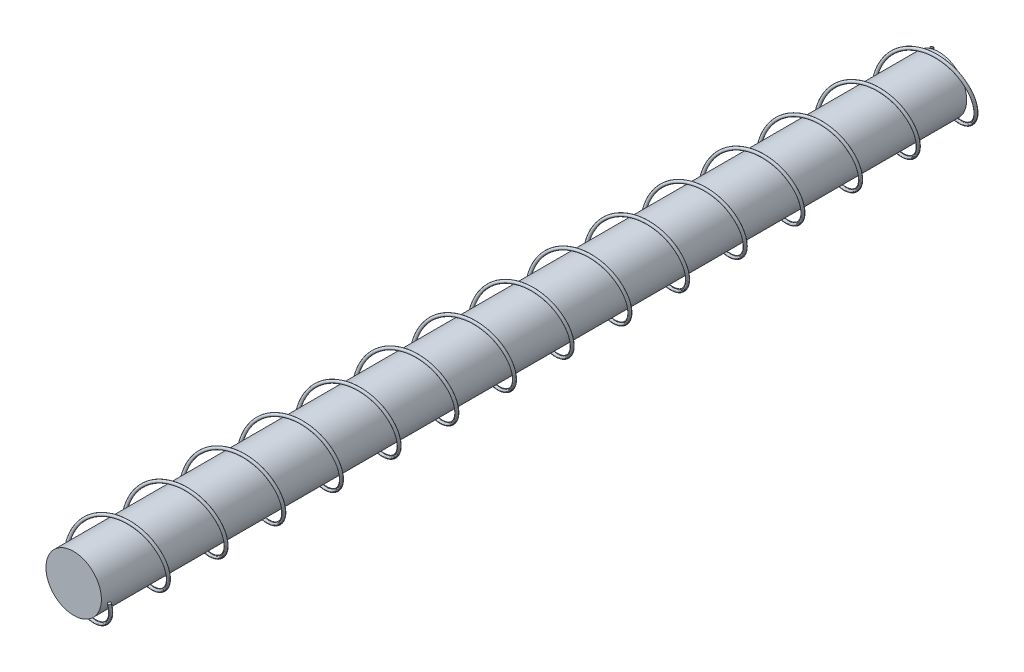
SolidWorks part; units mm, degrees
ref_plane "Ön Düzlem" through (0, 0, 0) normal (0, 0, 1) x (1, 0, 0)
ref_plane "Üst Düzlem" through (0, 0, 0) normal (0, 1, 0) x (1, 0, 0)
ref_plane "Sağ Düzlem" through (0, 0, 0) normal (1, 0, 0) x (0, 0, -1)
sketch "Çizim1" plane through (0, 0, 0) normal (0, 0, 1) x (1, 0, 0)
  circle A0 centre (0, 0) radius 0.9615
extrude "Yükseklik-Ekstrüzyon1" add sketch "Çizim1" along normal blind 30
sketch "Çizim3" plane through (0, 0, 30) normal (0, 0, 1) x (1, 0, 0)
  circle A0 centre (0, 0) radius 1.2377
curve "Helis/Spiral1" pitch 2 height 31 turns 15.5
ref_plane "Düzlem1" through (-1.2375, -0.0216, -1) normal (-0.0169, 0.9683, -0.2491) x (0.9999, 0.0164, -0.0042)
sketch "Çizim4" plane through (-1.2375, -0.0216, -1) normal (-0.0169, 0.9683, -0.2491) x (0.9999, 0.0164, -0.0042)
  circle A0 centre (0, 0) radius 0.0501
  spline S0 degree 3 poles (-1993.2342, 94.3185) (-8.8057, -58.5607) (4.8864, -32.4301) (2.1202, -29.6562) (2.0249, -29.5929) (1.7281, -29.4281) (1.5138, -29.3505) (1.0797, -29.2226) (0.8583, -29.1737) (0.4122, -29.0976) (0.1872, -29.0692) (-0.067, -29.056) (-0.0953, -29.0547) (-0.1254, -29.0543) (-0.1255, -29.0543) (-0.1184, -29.0543) (-0.106, -29.0541) (-0.0795, -29.0535) (-0.0583, -29.0528) (0.0123, -29.0498) (0.0688, -29.0461) (0.238, -29.0327) (0.3505, -29.0204) (0.6869, -28.9751) (0.9098, -28.934) (1.3491, -28.825) (1.5663, -28.758) (1.8763, -28.6197) (1.9772, -28.5672) (2.1634, -28.4387) (2.2518, -28.3624) (2.3343, -28.2141) (2.352, -28.1586) (2.3545, -28.0455) (2.3391, -27.9892) (2.2617, -27.8382) (2.1747, -27.7599) (1.9907, -27.6282) (1.8906, -27.5744) (1.6851, -27.4795) (1.5794, -27.4387) (1.2579, -27.3298) (1.0379, -27.2745) (0.594, -27.1864) (0.3697, -27.1535) (0.088, -27.1281) (0.0316, -27.1238) (-0.0532, -27.1193) (-0.0814, -27.118) (-0.1115, -27.1174) (-0.1132, -27.1174) (-0.1168, -27.1174) (-0.1172, -27.1174) (-0.1119, -27.1173) (-0.1013, -27.1172) (-0.0766, -27.1167) (-0.0554, -27.116) (0.0718, -27.1109) (0.1846, -27.1015) (0.5222, -27.0652) (0.746, -27.0296) (1.1884, -26.9344) (1.4075, -26.875) (1.7252, -26.7553) (1.8292, -26.7103) (2.0286, -26.6032) (2.1248, -26.5415) (2.2474, -26.424) (2.2844, -26.3805) (2.3406, -26.2822) (2.3592, -26.2271) (2.3638, -26.114) (2.3494, -26.0575) (2.2991, -25.9562) (2.264, -25.9109) (2.1459, -25.789) (2.051, -25.7249) (1.8538, -25.6139) (1.7504, -25.5671) (1.4347, -25.4426) (1.2163, -25.3804) (0.7751, -25.2797) (0.5517, -25.2415) (0.2147, -25.2011) (0.102, -25.1904) (-0.0393, -25.1826) (-0.0711, -25.1811) (-0.1029, -25.1805) (-0.1082, -25.1804) (-0.109, -25.1804) (-0.1055, -25.1804) (-0.0966, -25.1803) (-0.0736, -25.1799) (-0.0524, -25.1792) (0.0182, -25.1765) (0.0747, -25.173) (0.3567, -25.1512) (0.5813, -25.1208) (1.0263, -25.0381) (1.2469, -24.9856) (1.5699, -24.8812) (1.6763, -24.842) (1.8833, -24.7506) (1.9844, -24.6987) (2.1718, -24.5718) (2.2608, -24.4967) (2.3469, -24.3504) (2.3664, -24.2956) (2.373, -24.1826) (2.3595, -24.1258) (2.2861, -23.9728) (2.1999, -23.8932) (2.017, -23.7599) (1.9171, -23.7055) (1.6096, -23.5619) (1.3932, -23.492) (0.9554, -23.3774) (0.733, -23.3336) (0.3971, -23.2843) (0.2848, -23.2706) (0.1158, -23.2551) (0.0594, -23.2507) (-0.0254, -23.2459) (-0.0572, -23.2444) (-0.089, -23.2436) (-0.096, -23.2435) (-0.1025, -23.2435) (-0.0919, -23.2434) (-0.0848, -23.2433) (-0.0636, -23.2429) (-0.0495, -23.2425) (0.1908, -23.2336) (0.4161, -23.2076) (0.8631, -23.1368) (1.085, -23.0906) (1.5208, -22.9684) (1.7361, -22.8939) (2.0361, -22.7351) (2.1327, -22.674) (2.2568, -22.5582) (2.2946, -22.5153) (2.3531, -22.4185) (2.3734, -22.364) (2.382, -22.2512) (2.3696, -22.1941) (2.322, -22.0915) (2.2878, -22.0455) (2.1715, -21.9219) (2.077, -21.857) (1.7822, -21.6887) (1.5682, -21.61) (1.1347, -21.48) (0.9135, -21.4303) (0.4676, -21.3527) (0.2427, -21.324) (-0.0115, -21.3092) (-0.0397, -21.3078) (-0.0751, -21.3068) (-0.083, -21.3066) (-0.091, -21.3065) (-0.0928, -21.3065) (-0.0916, -21.3065) (-0.0854, -21.3065) (-0.066, -21.3062) (-0.0466, -21.3057) (0.0241, -21.3032) (0.0806, -21.2998) (0.2498, -21.2871) (0.3624, -21.2751) (0.699, -21.2309) (0.922, -21.1905) (1.3617, -21.0833) (1.5792, -21.0173) (1.8903, -20.8816) (1.9916, -20.8302) (2.18, -20.7048) (2.2697, -20.6308) (2.3592, -20.4866) (2.3804, -20.4324) (2.391, -20.3198) (2.3796, -20.2625) (2.3103, -20.1075) (2.225, -20.0266) (2.0433, -19.8917) (1.9437, -19.8367) (1.7391, -19.7401) (1.6336, -19.6986) (1.3127, -19.5879) (1.0929, -19.5318) (0.6493, -19.4421) (0.4252, -19.4085) (0.1436, -19.3821) (0.0871, -19.3776) (0.0024, -19.3725) (-0.0329, -19.3708) (-0.0682, -19.3698) (-0.0788, -19.3696) (-0.086, -19.3696) (-0.079, -19.3695) (-0.0613, -19.3694) (-0.0436, -19.3689) (0.0836, -19.3647) (0.1965, -19.3556) (0.5341, -19.3205) (0.758, -19.2856) (1.2008, -19.1919) (1.4201, -19.1335) (1.7386, -19.0159) (1.8429, -18.9716) (2.0435, -18.8668) (2.1405, -18.8064) (2.266, -18.6923) (2.3045, -18.65) (2.3652, -18.5546) (2.3872, -18.5008) (2.3998, -18.3884) (2.3895, -18.3309) (2.3448, -18.227) (2.3115, -18.1802) (2.1971, -18.0548) (2.103, -17.9892) (1.9072, -17.8757) (1.8042, -17.8281) (1.4893, -17.7014) (1.2712, -17.6383) (0.8303, -17.5359) (0.6071, -17.497) (0.2702, -17.4555) (0.1575, -17.4445) (0.0163, -17.4359) (-0.019, -17.4341) (-0.0579, -17.4329) (-0.0685, -17.4327) (-0.0738, -17.4326) (-0.076, -17.4326) (-0.0725, -17.4326) (-0.0565, -17.4325) (-0.0406, -17.4321) (0.0301, -17.4299) (0.0865, -17.4266) (0.3687, -17.4059) (0.5934, -17.3762) (1.0386, -17.295) (1.2594, -17.2433) (1.583, -17.1406) (1.6895, -17.1021) (1.8973, -17.0124) (1.9989, -16.9615) (2.1882, -16.8376) (2.2785, -16.7647) (2.3713, -16.6225) (2.394, -16.5692) (2.4086, -16.457) (2.3993, -16.3992) (2.3344, -16.2424) (2.2499, -16.1601) (2.0695, -16.0235) (1.9702, -15.968) (1.6639, -15.8216) (1.4479, -15.7507) (1.0105, -15.6343) (0.7882, -15.5898) (0.4525, -15.5393) (0.3402, -15.5253) (0.1713, -15.5091) (0.1149, -15.5045) (0.0302, -15.4992) (-0.0051, -15.4974) (-0.044, -15.4961) (-0.0564, -15.4958) (-0.0617, -15.4957) (-0.0652, -15.4957) (-0.0677, -15.4956) (-0.0518, -15.4956) (-0.0377, -15.4953) (0.2027, -15.4883) (0.428, -15.4624) (0.8753, -15.3932) (1.0974, -15.3476) (1.5337, -15.2275) (1.7493, -15.1541) (2.051, -14.9985) (2.1483, -14.9388) (2.2752, -14.8262) (2.3143, -14.7846) (2.3772, -14.6905) (2.4007, -14.6375) (2.4172, -14.5255) (2.409, -14.4677) (2.3673, -14.3625) (2.3349, -14.315) (2.2226, -14.1878) (2.1289, -14.1214) (1.8363, -13.9494) (1.6225, -13.8695) (1.1896, -13.7375) (0.9686, -13.6871) (0.5229, -13.608) (0.2981, -13.5787) (0.044, -13.5626) (0.0158, -13.561) (-0.0266, -13.5594) (-0.0407, -13.5589) (-0.0566, -13.5587) (-0.0595, -13.5587) (-0.0559, -13.5587) (-0.0506, -13.5586) (-0.0383, -13.5585) (-0.0277, -13.5582) (0.036, -13.5565) (0.0925, -13.5533) (0.2618, -13.5413) (0.3744, -13.5297) (0.7111, -13.4866) (0.9342, -13.4469) (1.3744, -13.3415) (1.5921, -13.2765) (1.9043, -13.1432) (2.0061, -13.0929) (2.1964, -12.9704) (2.2873, -12.8985) (2.383, -12.7584) (2.4073, -12.7058) (2.4258, -12.5942) (2.4187, -12.5361) (2.3583, -12.3775) (2.2748, -12.2937) (2.0957, -12.1554) (1.9967, -12.0993) (1.7929, -12.0008) (1.6877, -11.9586) (1.3675, -11.846) (1.1479, -11.7891) (0.7046, -11.6979) (0.4805, -11.6637) (0.199, -11.6361) (0.1144, -11.6291) (0.0297, -11.6244) (-0.0127, -11.6226) (-0.0286, -11.6221) (-0.0445, -11.6218) (-0.048, -11.6218) (-0.0512, -11.6217) (-0.0459, -11.6217) (-0.0353, -11.6216) (-0.0247, -11.6214) (0.0955, -11.6185) (0.2084, -11.6096) (0.5461, -11.5757) (0.7701, -11.5414) (1.2133, -11.4494) (1.4328, -11.3918) (1.7519, -11.2763) (1.8566, -11.2328) (2.0583, -11.1301) (2.156, -11.0711) (2.2843, -10.96) (2.324, -10.919) (2.3888, -10.8263) (2.4138, -10.7741) (2.4342, -10.6628) (2.4282, -10.6046) (2.3895, -10.4983) (2.3582, -10.45) (2.248, -10.3209) (2.1548, -10.2537) (1.9605, -10.1378) (1.8579, -10.0893) (1.5438, -9.9603) (1.326, -9.8963) (0.8855, -9.7923) (0.6624, -9.7527) (0.3256, -9.71) (0.213, -9.6986) (0.0718, -9.6893) (0.0436, -9.6877) (0.0012, -9.6859) (-0.0165, -9.6852) (-0.0341, -9.6849) (-0.0394, -9.6848) (-0.043, -9.6848) (-0.0395, -9.6848) (-0.0306, -9.6847) (-0.0218, -9.6846) (0.0418, -9.6832) (0.0984, -9.6801) (0.3806, -9.6606) (0.6053, -9.6316) (1.0509, -9.5518) (1.2718, -9.5009) (1.5959, -9.3999) (1.7027, -9.3621) (1.9112, -9.274) (2.0132, -9.2241) (2.2044, -9.1031) (2.2958, -9.0322) (2.3946, -8.8942) (2.4203, -8.8423) (2.4425, -8.7314) (2.4377, -8.6731) (2.4006, -8.5662) (2.3698, -8.5176) (2.2971, -8.4309) (2.2552, -8.3924) (2.1219, -8.2873) (2.0231, -8.2306) (1.7182, -8.0815) (1.5025, -8.0095) (1.0656, -7.8912) (0.8435, -7.846) (0.5079, -7.7944) (0.3395, -7.7728) (0.1422, -7.7559) (0.0434, -7.7502) (-0.0026, -7.7485) (-0.022, -7.748) (-0.0273, -7.7479) (-0.0308, -7.7478) (-0.0347, -7.7478) (-0.0259, -7.7478) (-0.0188, -7.7477) (0.1014, -7.7454) (0.2143, -7.7365) (0.4395, -7.7144) (0.5518, -7.7002) (0.8874, -7.6494) (1.1096, -7.6046) (1.5465, -7.4864) (1.7624, -7.4141) (2.0656, -7.2616) (2.1636, -7.2033) (2.2932, -7.0937) (2.3335, -7.0534) (2.4003, -6.962) (2.4267, -6.9105) (2.4508, -6.8) (2.447, -6.7416) (2.4116, -6.6341) (2.3813, -6.5851) (2.2734, -6.4541) (2.1806, -6.3861) (1.8903, -6.2102) (1.6768, -6.1292) (1.2446, -5.9951) (1.0237, -5.9439) (0.5783, -5.8633) (0.3536, -5.8334) (0.0996, -5.816) (0.0573, -5.8135) (0.0078, -5.8116) (-0.0134, -5.811) (-0.0223, -5.8109) (-0.0265, -5.8109) (-0.023, -5.8109) (-0.0177, -5.8108) (-0.0124, -5.8108) (0.0477, -5.8098) (0.1043, -5.8068) (0.2736, -5.7955) (0.3863, -5.7843) (0.7231, -5.7423) (0.9464, -5.7033) (1.3869, -5.5996) (1.6049, -5.5356) (1.9181, -5.4048) (2.0203, -5.3553) (2.2124, -5.2357) (2.3044, -5.1658) (2.4059, -5.0298) (2.433, -4.9787) (2.4589, -4.8686) (2.4563, -4.8101) (2.4225, -4.7021) (2.3928, -4.6527) (2.3217, -4.5648) (2.2802, -4.5258) (2.148, -4.4193) (2.0496, -4.362) (1.8468, -4.2616) (1.7418, -4.2187) (1.4223, -4.1043) (1.2029, -4.0465) (0.7599, -3.9538) (0.536, -3.9189) (0.2545, -3.8903) (0.17, -3.8829) (0.0711, -3.8769) (0.0217, -3.8748) (-0.0022, -3.8741) (-0.0119, -3.874) (-0.0154, -3.8739) (-0.0174, -3.8739) (-0.0129, -3.8739) (-0.0094, -3.8739) (0.1073, -3.8724) (0.2202, -3.8635) (0.5581, -3.8308) (0.7822, -3.7973) (1.2257, -3.7068) (1.4454, -3.6501) (1.7652, -3.5365) (1.8702, -3.4937) (2.0729, -3.3931) (2.1712, -3.3354) (2.3021, -3.2273) (2.3429, -3.1876) (2.4115, -3.0975) (2.4392, -3.0469) (2.4669, -2.9372) (2.4655, -2.8787) (2.4334, -2.7702) (2.4043, -2.7204) (2.2987, -2.5875) (2.2064, -2.5185) (2.0137, -2.4) (1.9115, -2.3506) (1.5984, -2.2194) (1.3808, -2.1544) (0.9407, -2.0487) (0.7177, -2.0084) (0.3811, -1.9646) (0.2685, -1.9528) (0.1274, -1.9428) (0.085, -1.9402) (0.0356, -1.9381) (0.0108, -1.9373) (-0.0007, -1.9371) (-0.0051, -1.937) (-0.0068, -1.937) (-0.0091, -1.937) (-0.0065, -1.937) (-0.0047, -1.9369) (0.0536, -1.9365) (0.1102, -1.9334) (0.3925, -1.9153) (0.6173, -1.8868) (1.0631, -1.8086) (1.2843, -1.7585) (1.717, -1.626) (1.9309, -1.5456) (2.2204, -1.3683) (2.3128, -1.2993) (2.417, -1.1653) (2.4453, -1.115) (2.4749, -1.0058) (2.4745, -0.9472) (2.4442, -0.8382) (2.4157, -0.7881) (2.3462, -0.6988) (2.3052, -0.6593) (2.1741, -0.5514) (2.076, -0.4935) (1.7725, -0.3414) (1.557, -0.2684) (1.1206, -0.1482) (0.8987, -0.1023) (0.5633, -0.0496) (0.4511, -0.0348) (0.2823, -0.0174) (0.1977, -0.0098) (0.0989, -0.0036) (0.0495, -0.0013) (0.0247, -0.0005) (0.0115, -0.0002) (0.0053, -0.0001) (-0.0614, 0.0008) (-9.3862, 0.0228) (1986.5063, -7.2266) knots -0.011073 -0.011073 -0.011073 -0.011073 0.000339 0.000339 0.000679 0.000679 0.001358 0.001358 0.002037 0.002037 0.002716 0.002716 0.0028 0.0028 0.002806 0.002806 0.002822 0.002843 0.002885 0.002885 0.003055 0.003055 0.003395 0.003395 0.004073 0.004073 0.004752 0.004752 0.005092 0.005092 0.005431 0.005431 0.005601 0.005601 0.005771 0.005771 0.00611 0.00611 0.00645 0.00645 0.006789 0.006789 0.007468 0.007468 0.008147 0.008147 0.008317 0.008317 0.008401 0.008401 0.008407 0.008407 0.008412 0.008412 0.008423 0.008444 0.008486 0.008486 0.008826 0.008826 0.009505 0.009505 0.010184 0.010184 0.010523 0.010523 0.010862 0.010862 0.011032 0.011032 0.011202 0.011202 0.011372 0.011372 0.011541 0.011541 0.011881 0.011881 0.01222 0.01222 0.012899 0.012899 0.013578 0.013578 0.013918 0.013918 0.014002 0.014013 0.014013 0.014018 0.014018 0.014024 0.014045 0.014087 0.014087 0.014257 0.014257 0.014936 0.014936 0.015615 0.015615 0.015954 0.015954 0.016294 0.016294 0.016633 0.016633 0.016803 0.016803 0.016973 0.016973 0.017312 0.017312 0.017652 0.017652 0.01833 0.01833 0.019009 0.019009 0.019349 0.019349 0.019519 0.019519 0.019603 0.019614 0.019614 0.019625 0.019625 0.019646 0.019646 0.019688 0.019688 0.020367 0.020367 0.021046 0.021046 0.021725 0.021725 0.022064 0.022064 0.022234 0.022234 0.022404 0.022404 0.022574 0.022574 0.022743 0.022743 0.023083 0.023083 0.023762 0.023762 0.024441 0.024441 0.025119 0.025119 0.025204 0.025204 0.025226 0.025228 0.025228 0.025231 0.025231 0.025247 0.025289 0.025289 0.025459 0.025459 0.025798 0.025798 0.026477 0.026477 0.027156 0.027156 0.027496 0.027496 0.027835 0.027835 0.028005 0.028005 0.028175 0.028175 0.028514 0.028514 0.028853 0.028853 0.029193 0.029193 0.029872 0.029872 0.030551 0.030551 0.03072 0.03072 0.030805 0.030827 0.030827 0.030837 0.030837 0.030848 0.03089 0.03089 0.03123 0.03123 0.031909 0.031909 0.032587 0.032587 0.032927 0.032927 0.033266 0.033266 0.033436 0.033436 0.033606 0.033606 0.033776 0.033776 0.033945 0.033945 0.034285 0.034285 0.034624 0.034624 0.035303 0.035303 0.035982 0.035982 0.036321 0.036321 0.036406 0.036428 0.036438 0.036438 0.036443 0.036443 0.036449 0.036491 0.036491 0.036661 0.036661 0.03734 0.03734 0.038019 0.038019 0.038358 0.038358 0.038698 0.038698 0.039037 0.039037 0.039207 0.039207 0.039376 0.039376 0.039716 0.039716 0.040055 0.040055 0.040734 0.040734 0.041413 0.041413 0.041753 0.041753 0.041922 0.041922 0.042007 0.042028 0.042039 0.042044 0.042044 0.04205 0.04205 0.042092 0.042092 0.042771 0.042771 0.04345 0.04345 0.044129 0.044129 0.044468 0.044468 0.044638 0.044638 0.044808 0.044808 0.044977 0.044977 0.045147 0.045147 0.045487 0.045487 0.046166 0.046166 0.046844 0.046844 0.047523 0.047523 0.047608 0.047608 0.047651 0.047651 0.047656 0.047656 0.047661 0.047672 0.047693 0.047693 0.047863 0.047863 0.048202 0.048202 0.048881 0.048881 0.04956 0.04956 0.0499 0.0499 0.050239 0.050239 0.050409 0.050409 0.050578 0.050578 0.050918 0.050918 0.051257 0.051257 0.051597 0.051597 0.052276 0.052276 0.052955 0.052955 0.053124 0.053209 0.053209 0.053252 0.053257 0.053257 0.053262 0.053262 0.053273 0.053294 0.053294 0.053634 0.053634 0.054312 0.054312 0.054991 0.054991 0.055331 0.055331 0.05567 0.05567 0.05584 0.05584 0.05601 0.05601 0.056179 0.056179 0.056349 0.056349 0.056689 0.056689 0.057028 0.057028 0.057707 0.057707 0.058386 0.058386 0.058725 0.058725 0.05881 0.05881 0.058853 0.058863 0.058863 0.058868 0.058868 0.058874 0.058895 0.058895 0.059065 0.059065 0.059744 0.059744 0.060423 0.060423 0.060762 0.060762 0.061101 0.061101 0.061441 0.061441 0.061611 0.061611 0.06178 0.06178 0.06195 0.06195 0.06212 0.06212 0.062459 0.062459 0.063138 0.063138 0.063817 0.063817 0.064157 0.064326 0.064411 0.064454 0.064464 0.064469 0.064469 0.064475 0.064475 0.064496 0.064496 0.064835 0.064835 0.065175 0.065175 0.065854 0.065854 0.066533 0.066533 0.066872 0.066872 0.067042 0.067042 0.067212 0.067212 0.067381 0.067381 0.067551 0.067551 0.067891 0.067891 0.068569 0.068569 0.069248 0.069248 0.069927 0.069927 0.070012 0.070055 0.070076 0.070076 0.070081 0.070081 0.070086 0.070097 0.070097 0.070267 0.070267 0.070606 0.070606 0.071285 0.071285 0.071964 0.071964 0.072303 0.072303 0.072643 0.072643 0.072813 0.072813 0.072982 0.072982 0.073152 0.073152 0.073322 0.073322 0.073661 0.073661 0.074001 0.074001 0.07468 0.07468 0.075358 0.075358 0.075528 0.075613 0.075655 0.075677 0.075685 0.075685 0.075687 0.075687 0.075698 0.075698 0.076037 0.076037 0.076716 0.076716 0.077395 0.077395 0.077735 0.077735 0.078074 0.078074 0.078244 0.078244 0.078414 0.078414 0.078583 0.078583 0.078753 0.078753 0.079092 0.079092 0.079432 0.079432 0.080111 0.080111 0.08079 0.08079 0.081129 0.081129 0.081214 0.081256 0.081278 0.081288 0.081291 0.081291 0.081294 0.081294 0.081299 0.081299 0.081469 0.081469 0.082148 0.082148 0.082826 0.082826 0.083505 0.083505 0.083845 0.083845 0.084015 0.084015 0.084184 0.084184 0.084354 0.084354 0.084524 0.084524 0.084863 0.084863 0.085542 0.085542 0.086221 0.086221 0.08656 0.08656 0.08673 0.086815 0.086857 0.086879 0.086889 0.086897 0.086897 0.087089 0.087089 0.087089 0.087089 only from (2.3449, -30.0336) to (0, 0) construction
  spline S1 degree 3 poles (2.3449, -30.0336) (2.3454, -29.9173) (2.28, -29.8164) (2.1202, -29.6562) (2.0249, -29.5929) (1.7281, -29.4281) (1.5138, -29.3505) (1.0797, -29.2226) (0.8583, -29.1737) (0.4122, -29.0976) (0.1872, -29.0692) (-0.067, -29.056) (-0.0953, -29.0547) (-0.1254, -29.0543) (-0.1255, -29.0543) (-0.1184, -29.0543) (-0.106, -29.0541) (-0.0795, -29.0535) (-0.0583, -29.0528) (0.0123, -29.0498) (0.0688, -29.0461) (0.238, -29.0327) (0.3505, -29.0204) (0.6869, -28.9751) (0.9098, -28.934) (1.3491, -28.825) (1.5663, -28.758) (1.8763, -28.6197) (1.9772, -28.5672) (2.1634, -28.4387) (2.2518, -28.3624) (2.3343, -28.2141) (2.352, -28.1586) (2.3545, -28.0455) (2.3391, -27.9892) (2.2617, -27.8382) (2.1747, -27.7599) (1.9907, -27.6282) (1.8906, -27.5744) (1.6851, -27.4795) (1.5794, -27.4387) (1.2579, -27.3298) (1.0379, -27.2745) (0.594, -27.1864) (0.3697, -27.1535) (0.088, -27.1281) (0.0316, -27.1238) (-0.0532, -27.1193) (-0.0814, -27.118) (-0.1115, -27.1174) (-0.1132, -27.1174) (-0.1168, -27.1174) (-0.1172, -27.1174) (-0.1119, -27.1173) (-0.1013, -27.1172) (-0.0766, -27.1167) (-0.0554, -27.116) (0.0718, -27.1109) (0.1846, -27.1015) (0.5222, -27.0652) (0.746, -27.0296) (1.1884, -26.9344) (1.4075, -26.875) (1.7252, -26.7553) (1.8292, -26.7103) (2.0286, -26.6032) (2.1248, -26.5415) (2.2474, -26.424) (2.2844, -26.3805) (2.3406, -26.2822) (2.3592, -26.2271) (2.3638, -26.114) (2.3494, -26.0575) (2.2991, -25.9562) (2.264, -25.9109) (2.1459, -25.789) (2.051, -25.7249) (1.8538, -25.6139) (1.7504, -25.5671) (1.4347, -25.4426) (1.2163, -25.3804) (0.7751, -25.2797) (0.5517, -25.2415) (0.2147, -25.2011) (0.102, -25.1904) (-0.0393, -25.1826) (-0.0711, -25.1811) (-0.1029, -25.1805) (-0.1082, -25.1804) (-0.109, -25.1804) (-0.1055, -25.1804) (-0.0966, -25.1803) (-0.0736, -25.1799) (-0.0524, -25.1792) (0.0182, -25.1765) (0.0747, -25.173) (0.3567, -25.1512) (0.5813, -25.1208) (1.0263, -25.0381) (1.2469, -24.9856) (1.5699, -24.8812) (1.6763, -24.842) (1.8833, -24.7506) (1.9844, -24.6987) (2.1718, -24.5718) (2.2608, -24.4967) (2.3469, -24.3504) (2.3664, -24.2956) (2.373, -24.1826) (2.3595, -24.1258) (2.2861, -23.9728) (2.1999, -23.8932) (2.017, -23.7599) (1.9171, -23.7055) (1.6096, -23.5619) (1.3932, -23.492) (0.9554, -23.3774) (0.733, -23.3336) (0.3971, -23.2843) (0.2848, -23.2706) (0.1158, -23.2551) (0.0594, -23.2507) (-0.0254, -23.2459) (-0.0572, -23.2444) (-0.089, -23.2436) (-0.096, -23.2435) (-0.1025, -23.2435) (-0.0919, -23.2434) (-0.0848, -23.2433) (-0.0636, -23.2429) (-0.0495, -23.2425) (0.1908, -23.2336) (0.4161, -23.2076) (0.8631, -23.1368) (1.085, -23.0906) (1.5208, -22.9684) (1.7361, -22.8939) (2.0361, -22.7351) (2.1327, -22.674) (2.2568, -22.5582) (2.2946, -22.5153) (2.3531, -22.4185) (2.3734, -22.364) (2.382, -22.2512) (2.3696, -22.1941) (2.322, -22.0915) (2.2878, -22.0455) (2.1715, -21.9219) (2.077, -21.857) (1.7822, -21.6887) (1.5682, -21.61) (1.1347, -21.48) (0.9135, -21.4303) (0.4676, -21.3527) (0.2427, -21.324) (-0.0115, -21.3092) (-0.0397, -21.3078) (-0.0751, -21.3068) (-0.083, -21.3066) (-0.091, -21.3065) (-0.0928, -21.3065) (-0.0916, -21.3065) (-0.0854, -21.3065) (-0.066, -21.3062) (-0.0466, -21.3057) (0.0241, -21.3032) (0.0806, -21.2998) (0.2498, -21.2871) (0.3624, -21.2751) (0.699, -21.2309) (0.922, -21.1905) (1.3617, -21.0833) (1.5792, -21.0173) (1.8903, -20.8816) (1.9916, -20.8302) (2.18, -20.7048) (2.2697, -20.6308) (2.3592, -20.4866) (2.3804, -20.4324) (2.391, -20.3198) (2.3796, -20.2625) (2.3103, -20.1075) (2.225, -20.0266) (2.0433, -19.8917) (1.9437, -19.8367) (1.7391, -19.7401) (1.6336, -19.6986) (1.3127, -19.5879) (1.0929, -19.5318) (0.6493, -19.4421) (0.4252, -19.4085) (0.1436, -19.3821) (0.0871, -19.3776) (0.0024, -19.3725) (-0.0329, -19.3708) (-0.0682, -19.3698) (-0.0788, -19.3696) (-0.086, -19.3696) (-0.079, -19.3695) (-0.0613, -19.3694) (-0.0436, -19.3689) (0.0836, -19.3647) (0.1965, -19.3556) (0.5341, -19.3205) (0.758, -19.2856) (1.2008, -19.1919) (1.4201, -19.1335) (1.7386, -19.0159) (1.8429, -18.9716) (2.0435, -18.8668) (2.1405, -18.8064) (2.266, -18.6923) (2.3045, -18.65) (2.3652, -18.5546) (2.3872, -18.5008) (2.3998, -18.3884) (2.3895, -18.3309) (2.3448, -18.227) (2.3115, -18.1802) (2.1971, -18.0548) (2.103, -17.9892) (1.9072, -17.8757) (1.8042, -17.8281) (1.4893, -17.7014) (1.2712, -17.6383) (0.8303, -17.5359) (0.6071, -17.497) (0.2702, -17.4555) (0.1575, -17.4445) (0.0163, -17.4359) (-0.019, -17.4341) (-0.0579, -17.4329) (-0.0685, -17.4327) (-0.0738, -17.4326) (-0.076, -17.4326) (-0.0725, -17.4326) (-0.0565, -17.4325) (-0.0406, -17.4321) (0.0301, -17.4299) (0.0865, -17.4266) (0.3687, -17.4059) (0.5934, -17.3762) (1.0386, -17.295) (1.2594, -17.2433) (1.583, -17.1406) (1.6895, -17.1021) (1.8973, -17.0124) (1.9989, -16.9615) (2.1882, -16.8376) (2.2785, -16.7647) (2.3713, -16.6225) (2.394, -16.5692) (2.4086, -16.457) (2.3993, -16.3992) (2.3344, -16.2424) (2.2499, -16.1601) (2.0695, -16.0235) (1.9702, -15.968) (1.6639, -15.8216) (1.4479, -15.7507) (1.0105, -15.6343) (0.7882, -15.5898) (0.4525, -15.5393) (0.3402, -15.5253) (0.1713, -15.5091) (0.1149, -15.5045) (0.0302, -15.4992) (-0.0051, -15.4974) (-0.044, -15.4961) (-0.0564, -15.4958) (-0.0617, -15.4957) (-0.0652, -15.4957) (-0.0677, -15.4956) (-0.0518, -15.4956) (-0.0377, -15.4953) (0.2027, -15.4883) (0.428, -15.4624) (0.8753, -15.3932) (1.0974, -15.3476) (1.5337, -15.2275) (1.7493, -15.1541) (2.051, -14.9985) (2.1483, -14.9388) (2.2752, -14.8262) (2.3143, -14.7846) (2.3772, -14.6905) (2.4007, -14.6375) (2.4172, -14.5255) (2.409, -14.4677) (2.3673, -14.3625) (2.3349, -14.315) (2.2226, -14.1878) (2.1289, -14.1214) (1.8363, -13.9494) (1.6225, -13.8695) (1.1896, -13.7375) (0.9686, -13.6871) (0.5229, -13.608) (0.2981, -13.5787) (0.044, -13.5626) (0.0158, -13.561) (-0.0266, -13.5594) (-0.0407, -13.5589) (-0.0566, -13.5587) (-0.0595, -13.5587) (-0.0559, -13.5587) (-0.0506, -13.5586) (-0.0383, -13.5585) (-0.0277, -13.5582) (0.036, -13.5565) (0.0925, -13.5533) (0.2618, -13.5413) (0.3744, -13.5297) (0.7111, -13.4866) (0.9342, -13.4469) (1.3744, -13.3415) (1.5921, -13.2765) (1.9043, -13.1432) (2.0061, -13.0929) (2.1964, -12.9704) (2.2873, -12.8985) (2.383, -12.7584) (2.4073, -12.7058) (2.4258, -12.5942) (2.4187, -12.5361) (2.3583, -12.3775) (2.2748, -12.2937) (2.0957, -12.1554) (1.9967, -12.0993) (1.7929, -12.0008) (1.6877, -11.9586) (1.3675, -11.846) (1.1479, -11.7891) (0.7046, -11.6979) (0.4805, -11.6637) (0.199, -11.6361) (0.1144, -11.6291) (0.0297, -11.6244) (-0.0127, -11.6226) (-0.0286, -11.6221) (-0.0445, -11.6218) (-0.048, -11.6218) (-0.0512, -11.6217) (-0.0459, -11.6217) (-0.0353, -11.6216) (-0.0247, -11.6214) (0.0955, -11.6185) (0.2084, -11.6096) (0.5461, -11.5757) (0.7701, -11.5414) (1.2133, -11.4494) (1.4328, -11.3918) (1.7519, -11.2763) (1.8566, -11.2328) (2.0583, -11.1301) (2.156, -11.0711) (2.2843, -10.96) (2.324, -10.919) (2.3888, -10.8263) (2.4138, -10.7741) (2.4342, -10.6628) (2.4282, -10.6046) (2.3895, -10.4983) (2.3582, -10.45) (2.248, -10.3209) (2.1548, -10.2537) (1.9605, -10.1378) (1.8579, -10.0893) (1.5438, -9.9603) (1.326, -9.8963) (0.8855, -9.7923) (0.6624, -9.7527) (0.3256, -9.71) (0.213, -9.6986) (0.0718, -9.6893) (0.0436, -9.6877) (0.0012, -9.6859) (-0.0165, -9.6852) (-0.0341, -9.6849) (-0.0394, -9.6848) (-0.043, -9.6848) (-0.0395, -9.6848) (-0.0306, -9.6847) (-0.0218, -9.6846) (0.0418, -9.6832) (0.0984, -9.6801) (0.3806, -9.6606) (0.6053, -9.6316) (1.0509, -9.5518) (1.2718, -9.5009) (1.5959, -9.3999) (1.7027, -9.3621) (1.9112, -9.274) (2.0132, -9.2241) (2.2044, -9.1031) (2.2958, -9.0322) (2.3946, -8.8942) (2.4203, -8.8423) (2.4425, -8.7314) (2.4377, -8.6731) (2.4006, -8.5662) (2.3698, -8.5176) (2.2971, -8.4309) (2.2552, -8.3924) (2.1219, -8.2873) (2.0231, -8.2306) (1.7182, -8.0815) (1.5025, -8.0095) (1.0656, -7.8912) (0.8435, -7.846) (0.5079, -7.7944) (0.3395, -7.7728) (0.1422, -7.7559) (0.0434, -7.7502) (-0.0026, -7.7485) (-0.022, -7.748) (-0.0273, -7.7479) (-0.0308, -7.7478) (-0.0347, -7.7478) (-0.0259, -7.7478) (-0.0188, -7.7477) (0.1014, -7.7454) (0.2143, -7.7365) (0.4395, -7.7144) (0.5518, -7.7002) (0.8874, -7.6494) (1.1096, -7.6046) (1.5465, -7.4864) (1.7624, -7.4141) (2.0656, -7.2616) (2.1636, -7.2033) (2.2932, -7.0937) (2.3335, -7.0534) (2.4003, -6.962) (2.4267, -6.9105) (2.4508, -6.8) (2.447, -6.7416) (2.4116, -6.6341) (2.3813, -6.5851) (2.2734, -6.4541) (2.1806, -6.3861) (1.8903, -6.2102) (1.6768, -6.1292) (1.2446, -5.9951) (1.0237, -5.9439) (0.5783, -5.8633) (0.3536, -5.8334) (0.0996, -5.816) (0.0573, -5.8135) (0.0078, -5.8116) (-0.0134, -5.811) (-0.0223, -5.8109) (-0.0265, -5.8109) (-0.023, -5.8109) (-0.0177, -5.8108) (-0.0124, -5.8108) (0.0477, -5.8098) (0.1043, -5.8068) (0.2736, -5.7955) (0.3863, -5.7843) (0.7231, -5.7423) (0.9464, -5.7033) (1.3869, -5.5996) (1.6049, -5.5356) (1.9181, -5.4048) (2.0203, -5.3553) (2.2124, -5.2357) (2.3044, -5.1658) (2.4059, -5.0298) (2.433, -4.9787) (2.4589, -4.8686) (2.4563, -4.8101) (2.4225, -4.7021) (2.3928, -4.6527) (2.3217, -4.5648) (2.2802, -4.5258) (2.148, -4.4193) (2.0496, -4.362) (1.8468, -4.2616) (1.7418, -4.2187) (1.4223, -4.1043) (1.2029, -4.0465) (0.7599, -3.9538) (0.536, -3.9189) (0.2545, -3.8903) (0.17, -3.8829) (0.0711, -3.8769) (0.0217, -3.8748) (-0.0022, -3.8741) (-0.0119, -3.874) (-0.0154, -3.8739) (-0.0174, -3.8739) (-0.0129, -3.8739) (-0.0094, -3.8739) (0.1073, -3.8724) (0.2202, -3.8635) (0.5581, -3.8308) (0.7822, -3.7973) (1.2257, -3.7068) (1.4454, -3.6501) (1.7652, -3.5365) (1.8702, -3.4937) (2.0729, -3.3931) (2.1712, -3.3354) (2.3021, -3.2273) (2.3429, -3.1876) (2.4115, -3.0975) (2.4392, -3.0469) (2.4669, -2.9372) (2.4655, -2.8787) (2.4334, -2.7702) (2.4043, -2.7204) (2.2987, -2.5875) (2.2064, -2.5185) (2.0137, -2.4) (1.9115, -2.3506) (1.5984, -2.2194) (1.3808, -2.1544) (0.9407, -2.0487) (0.7177, -2.0084) (0.3811, -1.9646) (0.2685, -1.9528) (0.1274, -1.9428) (0.085, -1.9402) (0.0356, -1.9381) (0.0108, -1.9373) (-0.0007, -1.9371) (-0.0051, -1.937) (-0.0068, -1.937) (-0.0091, -1.937) (-0.0065, -1.937) (-0.0047, -1.9369) (0.0536, -1.9365) (0.1102, -1.9334) (0.3925, -1.9153) (0.6173, -1.8868) (1.0631, -1.8086) (1.2843, -1.7585) (1.717, -1.626) (1.9309, -1.5456) (2.2204, -1.3683) (2.3128, -1.2993) (2.417, -1.1653) (2.4453, -1.115) (2.4749, -1.0058) (2.4745, -0.9472) (2.4442, -0.8382) (2.4157, -0.7881) (2.3462, -0.6988) (2.3052, -0.6593) (2.1741, -0.5514) (2.076, -0.4935) (1.7725, -0.3414) (1.557, -0.2684) (1.1206, -0.1482) (0.8987, -0.1023) (0.5633, -0.0496) (0.4511, -0.0348) (0.2823, -0.0174) (0.1977, -0.0098) (0.0989, -0.0036) (0.0495, -0.0013) (0.0247, -0.0005) (0.0115, -0.0002) (0.0053, -0.0001) (0.0018, 0) (-0.0009, 0) (0, 0) knots 0 0 0 0 0.000339 0.000339 0.000679 0.000679 0.001358 0.001358 0.002037 0.002037 0.002716 0.002716 0.0028 0.0028 0.002806 0.002806 0.002822 0.002843 0.002885 0.002885 0.003055 0.003055 0.003395 0.003395 0.004073 0.004073 0.004752 0.004752 0.005092 0.005092 0.005431 0.005431 0.005601 0.005601 0.005771 0.005771 0.00611 0.00611 0.00645 0.00645 0.006789 0.006789 0.007468 0.007468 0.008147 0.008147 0.008317 0.008317 0.008401 0.008401 0.008407 0.008407 0.008412 0.008412 0.008423 0.008444 0.008486 0.008486 0.008826 0.008826 0.009505 0.009505 0.010184 0.010184 0.010523 0.010523 0.010862 0.010862 0.011032 0.011032 0.011202 0.011202 0.011372 0.011372 0.011541 0.011541 0.011881 0.011881 0.01222 0.01222 0.012899 0.012899 0.013578 0.013578 0.013918 0.013918 0.014002 0.014013 0.014013 0.014018 0.014018 0.014024 0.014045 0.014087 0.014087 0.014257 0.014257 0.014936 0.014936 0.015615 0.015615 0.015954 0.015954 0.016294 0.016294 0.016633 0.016633 0.016803 0.016803 0.016973 0.016973 0.017312 0.017312 0.017652 0.017652 0.01833 0.01833 0.019009 0.019009 0.019349 0.019349 0.019519 0.019519 0.019603 0.019614 0.019614 0.019625 0.019625 0.019646 0.019646 0.019688 0.019688 0.020367 0.020367 0.021046 0.021046 0.021725 0.021725 0.022064 0.022064 0.022234 0.022234 0.022404 0.022404 0.022574 0.022574 0.022743 0.022743 0.023083 0.023083 0.023762 0.023762 0.024441 0.024441 0.025119 0.025119 0.025204 0.025204 0.025226 0.025228 0.025228 0.025231 0.025231 0.025247 0.025289 0.025289 0.025459 0.025459 0.025798 0.025798 0.026477 0.026477 0.027156 0.027156 0.027496 0.027496 0.027835 0.027835 0.028005 0.028005 0.028175 0.028175 0.028514 0.028514 0.028853 0.028853 0.029193 0.029193 0.029872 0.029872 0.030551 0.030551 0.03072 0.03072 0.030805 0.030827 0.030827 0.030837 0.030837 0.030848 0.03089 0.03089 0.03123 0.03123 0.031909 0.031909 0.032587 0.032587 0.032927 0.032927 0.033266 0.033266 0.033436 0.033436 0.033606 0.033606 0.033776 0.033776 0.033945 0.033945 0.034285 0.034285 0.034624 0.034624 0.035303 0.035303 0.035982 0.035982 0.036321 0.036321 0.036406 0.036428 0.036438 0.036438 0.036443 0.036443 0.036449 0.036491 0.036491 0.036661 0.036661 0.03734 0.03734 0.038019 0.038019 0.038358 0.038358 0.038698 0.038698 0.039037 0.039037 0.039207 0.039207 0.039376 0.039376 0.039716 0.039716 0.040055 0.040055 0.040734 0.040734 0.041413 0.041413 0.041753 0.041753 0.041922 0.041922 0.042007 0.042028 0.042039 0.042044 0.042044 0.04205 0.04205 0.042092 0.042092 0.042771 0.042771 0.04345 0.04345 0.044129 0.044129 0.044468 0.044468 0.044638 0.044638 0.044808 0.044808 0.044977 0.044977 0.045147 0.045147 0.045487 0.045487 0.046166 0.046166 0.046844 0.046844 0.047523 0.047523 0.047608 0.047608 0.047651 0.047651 0.047656 0.047656 0.047661 0.047672 0.047693 0.047693 0.047863 0.047863 0.048202 0.048202 0.048881 0.048881 0.04956 0.04956 0.0499 0.0499 0.050239 0.050239 0.050409 0.050409 0.050578 0.050578 0.050918 0.050918 0.051257 0.051257 0.051597 0.051597 0.052276 0.052276 0.052955 0.052955 0.053124 0.053209 0.053209 0.053252 0.053257 0.053257 0.053262 0.053262 0.053273 0.053294 0.053294 0.053634 0.053634 0.054312 0.054312 0.054991 0.054991 0.055331 0.055331 0.05567 0.05567 0.05584 0.05584 0.05601 0.05601 0.056179 0.056179 0.056349 0.056349 0.056689 0.056689 0.057028 0.057028 0.057707 0.057707 0.058386 0.058386 0.058725 0.058725 0.05881 0.05881 0.058853 0.058863 0.058863 0.058868 0.058868 0.058874 0.058895 0.058895 0.059065 0.059065 0.059744 0.059744 0.060423 0.060423 0.060762 0.060762 0.061101 0.061101 0.061441 0.061441 0.061611 0.061611 0.06178 0.06178 0.06195 0.06195 0.06212 0.06212 0.062459 0.062459 0.063138 0.063138 0.063817 0.063817 0.064157 0.064326 0.064411 0.064454 0.064464 0.064469 0.064469 0.064475 0.064475 0.064496 0.064496 0.064835 0.064835 0.065175 0.065175 0.065854 0.065854 0.066533 0.066533 0.066872 0.066872 0.067042 0.067042 0.067212 0.067212 0.067381 0.067381 0.067551 0.067551 0.067891 0.067891 0.068569 0.068569 0.069248 0.069248 0.069927 0.069927 0.070012 0.070055 0.070076 0.070076 0.070081 0.070081 0.070086 0.070097 0.070097 0.070267 0.070267 0.070606 0.070606 0.071285 0.071285 0.071964 0.071964 0.072303 0.072303 0.072643 0.072643 0.072813 0.072813 0.072982 0.072982 0.073152 0.073152 0.073322 0.073322 0.073661 0.073661 0.074001 0.074001 0.07468 0.07468 0.075358 0.075358 0.075528 0.075613 0.075655 0.075677 0.075685 0.075685 0.075687 0.075687 0.075698 0.075698 0.076037 0.076037 0.076716 0.076716 0.077395 0.077395 0.077735 0.077735 0.078074 0.078074 0.078244 0.078244 0.078414 0.078414 0.078583 0.078583 0.078753 0.078753 0.079092 0.079092 0.079432 0.079432 0.080111 0.080111 0.08079 0.08079 0.081129 0.081129 0.081214 0.081256 0.081278 0.081288 0.081291 0.081291 0.081294 0.081294 0.081299 0.081299 0.081469 0.081469 0.082148 0.082148 0.082826 0.082826 0.083505 0.083505 0.083845 0.083845 0.084015 0.084015 0.084184 0.084184 0.084354 0.084354 0.084524 0.084524 0.084863 0.084863 0.085542 0.085542 0.086221 0.086221 0.08656 0.08656 0.08673 0.086815 0.086857 0.086879 0.086889 0.086897 0.086897 0.0869 0.0869 0.0869 0.0869
  point P2 (0, 0)
  point P5 (0, 0)
sweep "Süpür1" add profiles "Çizim4" path "Helis/Spiral1"
